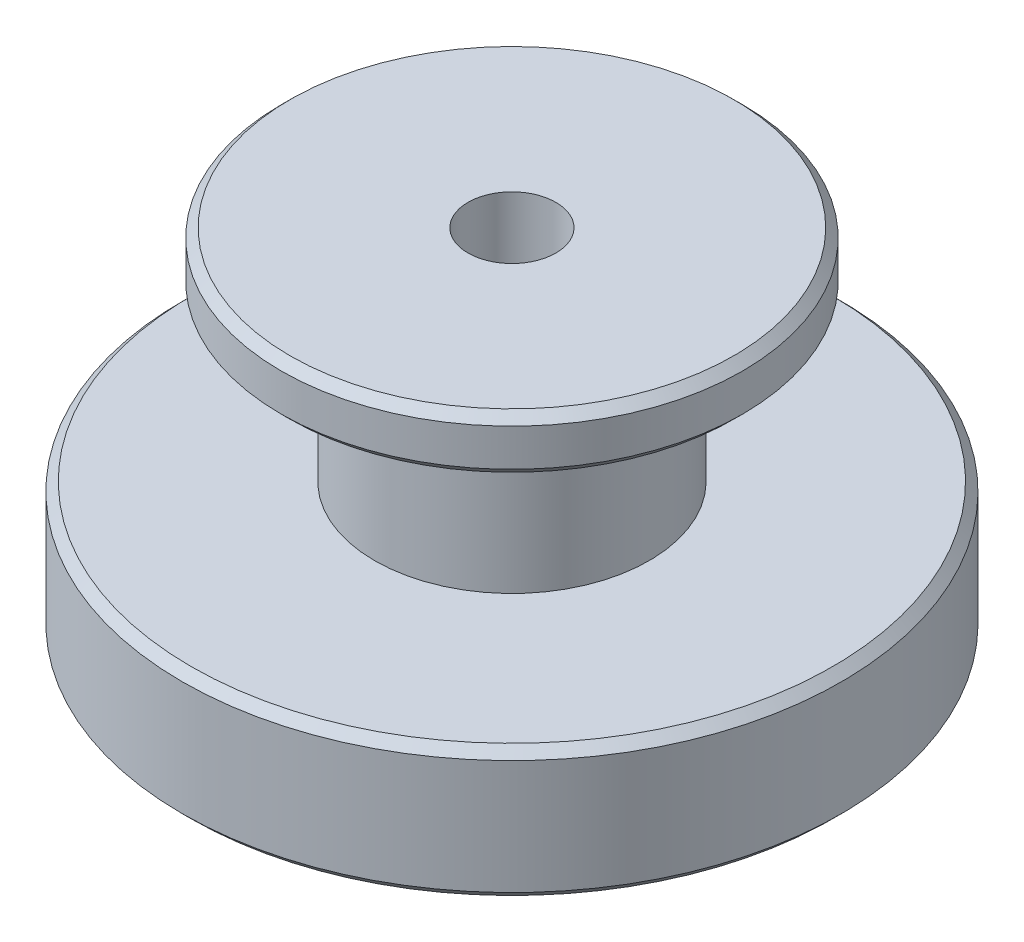
SolidWorks part; units mm, degrees
ref_plane "Alzado" through (0, 0, 0) normal (0, 0, 1) x (1, 0, 0)
ref_plane "Planta" through (0, 0, 0) normal (0, 1, 0) x (1, 0, 0)
ref_plane "Vista lateral" through (0, 0, 0) normal (1, 0, 0) x (0, 0, -1)
sketch "Croquis1" plane through (0, 0, 0) normal (0, 0, 1) x (1, 0, 0)
  line L0 (0, 175.8037) -> (0, 0) construction
  line L1 (4, 0) -> (29.2, 0)
  line L2 (30, 0.8) -> (30, 11.2)
  line L3 (29.2, 12) -> (12.5, 12)
  line L4 (12.5, 12) -> (12.5, 27)
  line L5 (12.5, 27) -> (20.2, 27)
  line L6 (21, 27.8) -> (21, 31.2)
  line L7 (20.2, 32) -> (4, 32)
  line L8 (4, 32) -> (4, 0)
  line L9 (21, 31.2) -> (20.2, 32)
  line L10 (20.2, 27) -> (21, 27.8)
  line L11 (30, 11.2) -> (29.2, 12)
  line L12 (29.2, 0) -> (30, 0.8)
  point P4 (30, 0)
  point P6 (30, 12)
  point P9 (21, 27)
  point P10 (21, 32)
  dimension "D1" = 8
  dimension "D2" = 12
  dimension "D3" = 5
  dimension "D4" = 15
  dimension "D5" = 60
  dimension "D6" = 42
  dimension "D7" = 25
  dimension "D8" = 0.8
  dimension "D9" = 45
  dimension "D10" = 0.8
  dimension "D11" = 45
  dimension "D12" = 0.8
  dimension "D13" = 45
  dimension "D14" = 0.8
  dimension "D15" = 45
revolve "Revolución1" add sketch "Croquis1" angle 360 about L0
